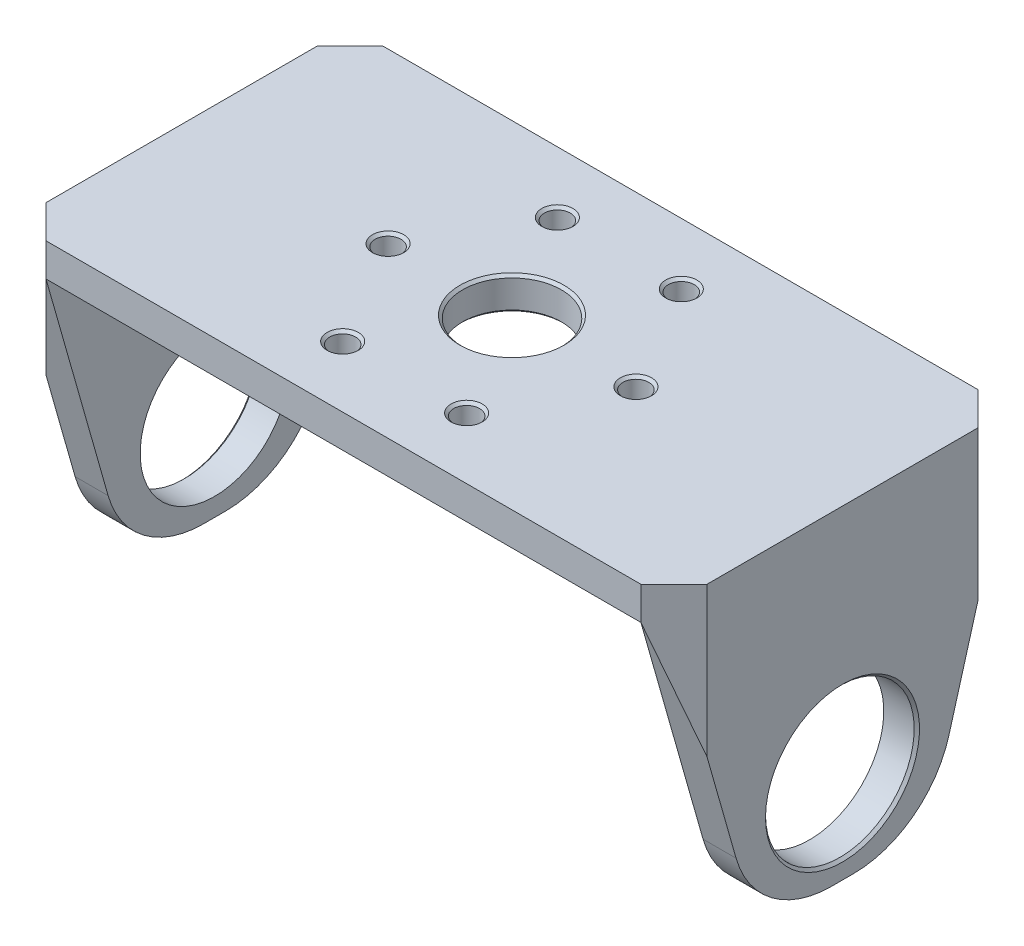
SolidWorks part; units mm, degrees
ref_plane "Front" through (0, 0, 0) normal (0, 0, 1) x (1, 0, 0)
ref_plane "Top" through (0, 0, 0) normal (0, 1, 0) x (1, 0, 0)
ref_plane "Right" through (0, 0, 0) normal (1, 0, 0) x (0, 0, -1)
ref_plane "Plane1" through (0, 6.35, 0) normal (0, 1, 0) x (1, 0, 0)
sketch "Sketch1" plane through (0, 6.35, 0) normal (0, 1, 0) x (1, 0, 0)
  line L0 (-57.15, -32.385) -> (57.15, -32.385)
  line L1 (57.15, -32.385) -> (57.15, 32.385)
  line L2 (57.15, 32.385) -> (-57.15, 32.385)
  line L3 (-57.15, 32.385) -> (-57.15, -32.385)
extrude "Boss-Extrude1" add sketch "Sketch1" against normal blind 6.35
sketch "Sketch2" plane through (57.15, 0, 0) normal (1, 0, 0) x (0, 0, -1)
  line L0 (-32.385, 6.35) -> (32.385, 6.35)
  line L1 (32.385, 6.35) -> (32.385, 0)
  line L2 (32.385, 0) -> (16.51, -55.88)
  line L3 (16.51, -55.88) -> (-16.51, -55.88)
  line L4 (-16.51, -55.88) -> (-32.385, 0)
  line L5 (-32.385, 0) -> (-32.385, 6.35)
extrude "Boss-Extrude2" add sketch "Sketch2" along normal blind 6.35
sketch "Sketch3" plane through (-57.15, 0, 0) normal (-1, 0, 0) x (0, 0, 1)
  line L0 (32.385, 0) -> (16.51, -55.88)
  line L1 (16.51, -55.88) -> (-16.51, -55.88)
  line L2 (-16.51, -55.88) -> (-32.385, 0)
  line L3 (-32.385, 0) -> (-32.385, 6.35)
  line L4 (-32.385, 6.35) -> (32.385, 6.35)
  line L5 (32.385, 6.35) -> (32.385, 0)
extrude "Boss-Extrude3" add sketch "Sketch3" along normal blind 6.35
hole_wizard "Hole1" positions "Sketch5" profile "Sketch4" legacy
sketch "Sketch5" plane through (0, 0, 0) normal (0, -1, 0) x (-1, 0, 0)
  point P0 (0, 0)
sketch "Sketch4" plane through (0, 0, 0) normal (1, 0, 0) x (0, 0, -1)
  line L0 (0, 0) -> (0, 6.35)
  line L1 (0, 6.35) -> (9.4869, 6.35)
  line L2 (9.4869, 6.35) -> (9.4869, 0)
  line L3 (9.4869, 0) -> (0, 0)
  line L4 (0, 110) -> (0, -10) construction
  dimension "Diameter" = 18.9738
  dimension "Depth" = 6.35
hole_wizard "#9 (0.196) Diameter Hole1" positions "Sketch7" profile "Sketch6" hole size "#9" standard "ANSI Inch"
sketch "Sketch7" plane through (0, 6.35, 0) normal (0, 1, 0) x (1, 0, 0)
  point P0 (11.9062, 20.6222)
sketch "Sketch6" plane through (11.9062, 6.35, -20.6222) normal (1, 0, 0) x (0, 0, 1)
  line L0 (0, 0) -> (0, 62.23)
  line L1 (0, 62.23) -> (2.4892, 62.23)
  line L2 (2.4892, 62.23) -> (2.4892, 0)
  line L5 (2.4892, 0) -> (0, 0)
  line L11 (0, -6.35) -> (0, 107.95) construction
  dimension "Thru Hole Dia." = 4.9784
  dimension "Thru Hole Depth" = 62.23
hole_wizard "#9 (0.196) Diameter Hole2" positions "Sketch9" profile "Sketch8" hole size "#9" standard "ANSI Inch"
sketch "Sketch9" plane through (0, 0, 0) normal (0, -1, 0) x (-1, 0, 0)
  point P0 (-23.8125, 0)
  point P1 (-11.9062, -20.6222)
  point P2 (11.9062, -20.6222)
  point P3 (23.8125, 0)
  point P4 (11.9062, 20.6222)
sketch "Sketch8" plane through (23.8125, 0, 0) normal (1, 0, 0) x (0, 0, -1)
  line L0 (0, 0) -> (0, 6.35)
  line L1 (0, 6.35) -> (2.4892, 6.35)
  line L2 (2.4892, 6.35) -> (2.4892, 0)
  line L5 (2.4892, 0) -> (0, 0)
  line L11 (0, -6.35) -> (0, 107.95) construction
  dimension "Thru Hole Dia." = 4.9784
  dimension "Thru Hole Depth" = 6.35
hole_wizard "Hole2" positions "Sketch11" profile "Sketch10" legacy
sketch "Sketch11" plane through (-63.5, 0, 0) normal (-1, 0, 0) x (0, 0, 1)
  point P0 (0, -38.1)
sketch "Sketch10" plane through (-63.5, -38.1, 0) normal (0, 1, 0) x (0, 0, 1)
  line L0 (0, 0) -> (0, 6.35)
  line L1 (0, 6.35) -> (14.2875, 6.35)
  line L2 (14.2875, 6.35) -> (14.2875, 0)
  line L3 (14.2875, 0) -> (0, 0)
  line L4 (0, 110) -> (0, -10) construction
  dimension "Diameter" = 28.575
  dimension "Depth" = 6.35
hole_wizard "Hole3" positions "Sketch13" profile "Sketch12" legacy
sketch "Sketch13" plane through (63.5, 0, 0) normal (1, 0, 0) x (0, 0, -1)
  point P0 (0, -38.1)
sketch "Sketch12" plane through (63.5, -38.1, 0) normal (0, 1, 0) x (0, 0, -1)
  line L0 (0, 0) -> (0, 127)
  line L1 (0, 127) -> (14.2875, 127)
  line L2 (14.2875, 127) -> (14.2875, 0)
  line L3 (14.2875, 0) -> (0, 0)
  line L4 (0, 110) -> (0, -10) construction
  dimension "Diameter" = 28.575
  dimension "Depth" = 127
chamfer "Chamfer1" distance 6.35 angle 45 4 edges at (63.5, 3.175, -32.385) (63.5, 3.175, 32.385) (-63.5, 3.175, -32.385) (-63.5, 3.175, 32.385)
chamfer "Chamfer2" distance 0.508 angle 45 16 edges at (0, 6.35, -9.4869) (-11.9062, 6.35, 18.133) (23.8125, 6.35, -2.4892) (11.9062, 0, -18.133) (-11.9062, 6.35, -23.1114) (0, 0, -9.4869) (-11.9062, 0, -23.1114) (63.5, -38.1, -14.2875) (11.9062, 6.35, 18.133) (-63.5, -38.1, 14.2875) (-23.8125, 6.35, -2.4892) (11.9062, 6.35, -18.133) (11.9062, 0, 18.133) (-23.8125, 0, -2.4892) (-11.9062, 0, 18.133) (23.8125, 0, -2.4892)
fillet "Fillet1" radius 19.05 4 edges at (60.325, -55.88, 16.51) (-60.325, -55.88, 16.51) (60.325, -55.88, -16.51) (-60.325, -55.88, -16.51)
